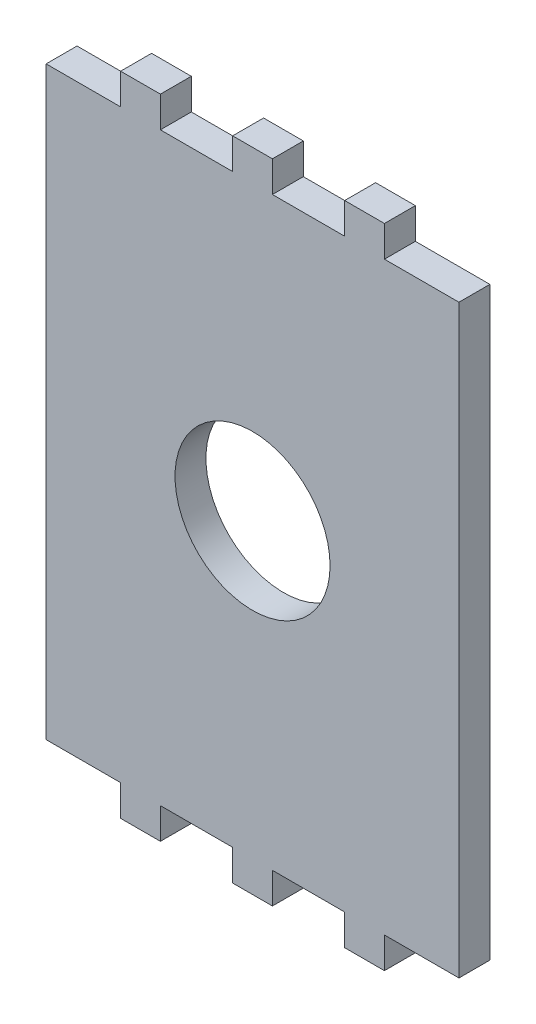
SolidWorks part; units mm, degrees
ref_plane "Front Plane" through (0, 0, 0) normal (0, 0, 1) x (1, 0, 0)
ref_plane "Top Plane" through (0, 0, 0) normal (0, 1, 0) x (1, 0, 0)
ref_plane "Right Plane" through (0, 0, 0) normal (1, 0, 0) x (0, 0, -1)
sketch "Sketch1" plane through (0, 0, 0) normal (0, 0, 1) x (1, 0, 0)
  line L0 (-21.15, 12.3) -> (21.15, 12.3) construction
  line L1 (-21.15, 30) -> (21.15, 30)
  line L2 (-21.15, 30) -> (-21.15, -30)
  line L3 (-21.15, -30) -> (21.15, -30)
  line L4 (21.15, 30) -> (21.15, -30)
  line L5 (2, -33.175) -> (2, -30)
  line L6 (-13.5, -30) -> (-9.5, -30)
  line L7 (-13.5, -30) -> (-13.5, -33.175)
  line L8 (-13.5, -33.175) -> (-9.5, -33.175)
  line L9 (-9.5, -30) -> (-9.5, -33.175)
  line L10 (2, -33.175) -> (-2, -33.175)
  line L11 (2, -30) -> (-2, -30)
  line L12 (-2, -33.175) -> (-2, -30)
  line L13 (2, -33.175) -> (-2, -30) construction
  line L14 (2, -30) -> (-2, -33.175) construction
  line L15 (-21.15, 0) -> (21.15, 0) construction
  line L16 (13.5, -30) -> (9.5, -30)
  line L17 (13.5, -30) -> (13.5, -33.175)
  line L18 (13.5, -33.175) -> (9.5, -33.175)
  line L19 (9.5, -30) -> (9.5, -33.175)
  line L20 (2, 30) -> (-2, 33.175) construction
  line L21 (2, 33.175) -> (-2, 30) construction
  line L22 (9.5, 30) -> (9.5, 33.175)
  line L23 (13.5, 33.175) -> (9.5, 33.175)
  line L24 (13.5, 30) -> (13.5, 33.175)
  line L25 (-2, 33.175) -> (-2, 30)
  line L26 (2, 33.175) -> (-2, 33.175)
  line L27 (-9.5, 30) -> (-9.5, 33.175)
  line L28 (-13.5, 33.175) -> (-9.5, 33.175)
  line L29 (-13.5, 30) -> (-13.5, 33.175)
  line L30 (2, 33.175) -> (2, 30)
  line L31 (-13.5, 31.5875) -> (13.5, 31.5875)
  circle A0 centre (0, 0) radius 8
  point P13 (0, -30)
  point P14 (0, -31.5875)
  point P37 (0, 31.5875)
  point P41 (0, 31.5875)
  dimension "D6" = 16
  dimension "D1" = 42.3
  dimension "D3" = 42.3
  dimension "D4" = 30
  dimension "D5" = 21.15
  dimension "D2" = 60
  dimension "D8" = 4
  dimension "D9" = 3.175
  dimension "D7" = 7.5
  dimension "D10" = 7.5
extrude "Boss-Extrude1" add sketch "Sketch1" along normal blind 3.175 contours L4 L1 L2 L3 A0 | L31 L29 L1 L27 | L29 L31 L27 L28 | L25 L31 L30 L26 | L31 L25 L1 L30 | L22 L31 L24 L23 | L31 L22 L1 L24 | L9 L3 L7 L8 | L12 L10 L5 L3 | L3 L19 L18 L17
sketch "Sketch2" plane through (0, 0, 3.175) normal (0, 0, 1) x (1, 0, 0)
  line L56 (21.1906, -30.0406) -> (21.1906, 30.0406)
  line L57 (21.1906, 30.0406) -> (13.5406, 30.0406)
  line L58 (13.5406, 30.0406) -> (13.5406, 33.2156)
  line L59 (13.5406, 33.2156) -> (9.4594, 33.2156)
  line L60 (9.4594, 33.2156) -> (9.4594, 30.0406)
  line L61 (9.4594, 30.0406) -> (2.0406, 30.0406)
  line L62 (2.0406, 30.0406) -> (2.0406, 33.2156)
  line L63 (2.0406, 33.2156) -> (-2.0406, 33.2156)
  line L64 (-2.0406, 33.2156) -> (-2.0406, 30.0406)
  line L65 (-2.0406, 30.0406) -> (-9.4594, 30.0406)
  line L66 (-9.4594, 30.0406) -> (-9.4594, 33.2156)
  line L67 (-9.4594, 33.2156) -> (-13.5406, 33.2156)
  line L68 (-13.5406, 33.2156) -> (-13.5406, 30.0406)
  line L69 (-13.5406, 30.0406) -> (-21.1906, 30.0406)
  line L70 (-21.1906, 30.0406) -> (-21.1906, -30.0406)
  line L71 (-21.1906, -30.0406) -> (-13.5406, -30.0406)
  line L72 (-13.5406, -30.0406) -> (-13.5406, -33.2156)
  line L73 (-13.5406, -33.2156) -> (-9.4594, -33.2156)
  line L74 (-9.4594, -33.2156) -> (-9.4594, -30.0406)
  line L75 (-9.4594, -30.0406) -> (-2.0406, -30.0406)
  line L76 (-2.0406, -30.0406) -> (-2.0406, -33.2156)
  line L77 (-2.0406, -33.2156) -> (2.0406, -33.2156)
  line L78 (2.0406, -33.2156) -> (2.0406, -30.0406)
  line L79 (2.0406, -30.0406) -> (9.4594, -30.0406)
  line L80 (9.4594, -30.0406) -> (9.4594, -33.2156)
  line L81 (9.4594, -33.2156) -> (13.5406, -33.2156)
  line L82 (13.5406, -33.2156) -> (13.5406, -30.0406)
  line L83 (13.5406, -30.0406) -> (21.1906, -30.0406)
  line L84 (21.1906, -30.0406) -> (21.1906, 30.0406)
  line L85 (21.1906, 30.0406) -> (13.5406, 30.0406)
  line L86 (13.5406, 30.0406) -> (13.5406, 33.2156)
  line L87 (13.5406, 33.2156) -> (9.4594, 33.2156)
  line L88 (9.4594, 33.2156) -> (9.4594, 30.0406)
  line L89 (9.4594, 30.0406) -> (2.0406, 30.0406)
  line L90 (2.0406, 30.0406) -> (2.0406, 33.2156)
  line L91 (2.0406, 33.2156) -> (-2.0406, 33.2156)
  line L92 (-2.0406, 33.2156) -> (-2.0406, 30.0406)
  line L93 (-2.0406, 30.0406) -> (-9.4594, 30.0406)
  line L94 (-9.4594, 30.0406) -> (-9.4594, 33.2156)
  line L95 (-9.4594, 33.2156) -> (-13.5406, 33.2156)
  line L96 (-13.5406, 33.2156) -> (-13.5406, 30.0406)
  line L97 (-13.5406, 30.0406) -> (-21.1906, 30.0406)
  line L98 (-21.1906, 30.0406) -> (-21.1906, -30.0406)
  line L99 (-21.1906, -30.0406) -> (-13.5406, -30.0406)
  line L100 (-13.5406, -30.0406) -> (-13.5406, -33.2156)
  line L101 (-13.5406, -33.2156) -> (-9.4594, -33.2156)
  line L102 (-9.4594, -33.2156) -> (-9.4594, -30.0406)
  line L103 (-9.4594, -30.0406) -> (-2.0406, -30.0406)
  line L104 (-2.0406, -30.0406) -> (-2.0406, -33.2156)
  line L105 (-2.0406, -33.2156) -> (2.0406, -33.2156)
  line L106 (2.0406, -33.2156) -> (2.0406, -30.0406)
  line L107 (2.0406, -30.0406) -> (9.4594, -30.0406)
  line L108 (9.4594, -30.0406) -> (9.4594, -33.2156)
  line L109 (9.4594, -33.2156) -> (13.5406, -33.2156)
  line L110 (13.5406, -33.2156) -> (13.5406, -30.0406)
  line L111 (13.5406, -30.0406) -> (21.1906, -30.0406)
  circle A2 centre (0, 0) radius 7.9594
  circle A3 centre (0, 0) radius 7.9594
  dimension "D1" = 0.0406
  dimension "D2" = 0.0406
extrude "Boss-Extrude3" add sketch "Sketch2" against normal blind 3.175
equation "\"stepper width\"=4.23"
equation "\"stepper hole disctance\" = 3.1"
equation "\"stepper hole diameter\"=0.34"
equation "\"stepper shaft hole\"=2.4"
equation "\"tooth width\"=0.4"
equation "\"tooth thickness\"=0.3175"
equation "\"tooth to side\"=0.75"
equation "\"motor chamber height\"= 6"
equation "\"D1@Sketch1\"=\"stepper width\""
equation "\"D3@Sketch1\"=\"stepper width\""
equation "\"D5@Sketch1\"=\"stepper width\"/2"
equation "\"gear shaft diameter\"=1.6"
equation "\"D6@Sketch1\"=\"gear shaft diameter\""
equation "\"D2@Sketch1\"=\"motor chamber height\""
equation "\"D8@Sketch1\"=\"tooth width\""
equation "\"D9@Sketch1\"=\"tooth thickness\""
equation "\"D1@Boss-Extrude1\"=\"tooth thickness\""
equation "\"D7@Sketch1\"=.75"
equation "\"D10@Sketch1\"=.75"
equation "\"D5@Sketch1\"=\"stepper hole diameter\""
